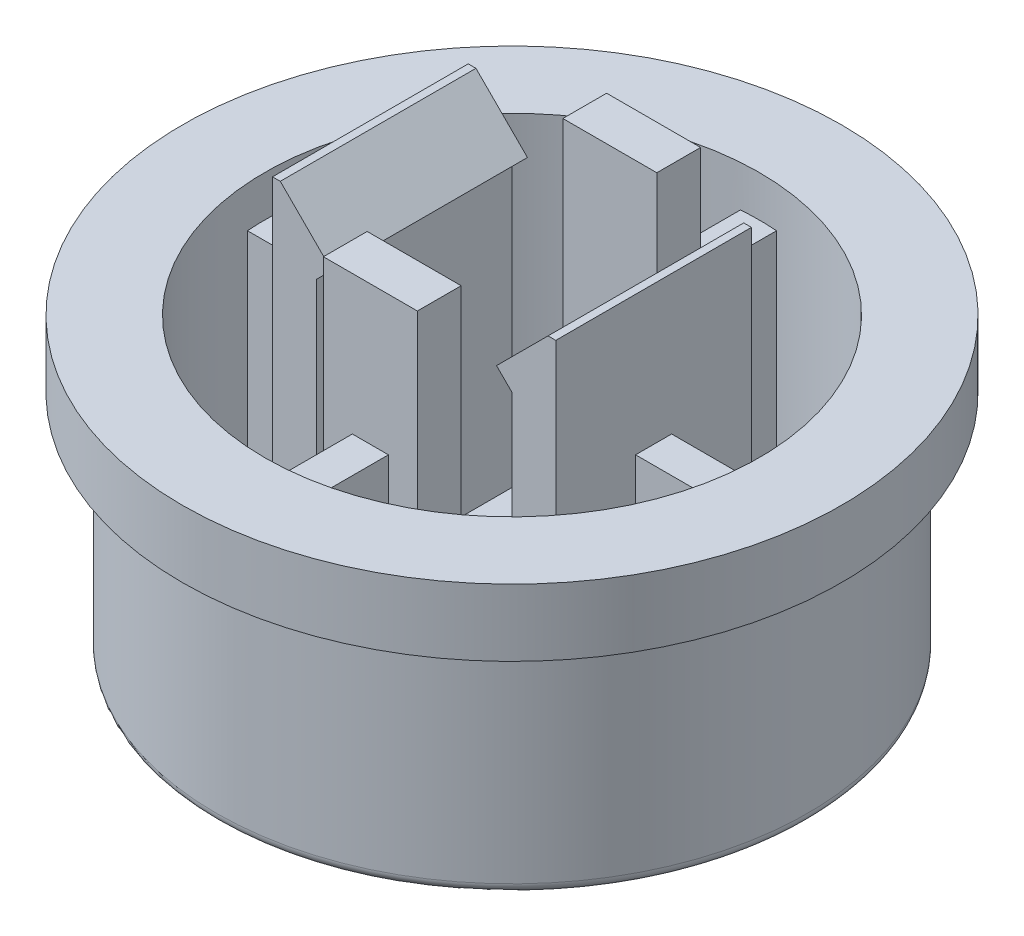
SolidWorks part; units mm, degrees
ref_plane "Front" through (0, 0, 0) normal (0, 0, 1) x (1, 0, 0)
ref_plane "Top" through (0, 0, 0) normal (0, 1, 0) x (1, 0, 0)
ref_plane "Right" through (0, 0, 0) normal (1, 0, 0) x (0, 0, -1)
sketch "Эскиз1" plane through (0, 0, 0) normal (0, 1, 0) x (1, 0, 0)
  circle A0 centre (0, 0) radius 5.75
extrude "Бобышка-Вытянуть1" add sketch "Эскиз1" along normal blind 0.9
sketch "Эскиз2" plane through (0, 0.9, 0) normal (0, 1, 0) x (1, 0, 0)
  circle A0 centre (0, 0) radius 5.75
  circle A1 centre (0, 0) radius 4.8
extrude "Бобышка-Вытянуть2" add sketch "Эскиз2" along normal blind 3.5
sketch "Эскиз3" plane through (0, 4.4, 0) normal (0, 1, 0) x (1, 0, 0)
  circle A0 centre (0, 0) radius 4.8
  circle A1 centre (0, 0) radius 6.4
extrude "Бобышка-Вытянуть3" add sketch "Эскиз3" along normal blind 1.3
sketch "Эскиз4" plane through (0, 0.9, 0) normal (0, 1, 0) x (1, 0, 0)
  line L2 (-2.75, -1.9) -> (-2.75, 1.9)
  line L4 (2.75, -1.9) -> (2.75, 1.9)
  line L8 (-1.9, -1.9) -> (-1.9, 1.9)
  line L10 (1.9, -1.9) -> (1.9, 1.9)
  line L11 (-0.9124, 1.9) -> (0.9124, 1.9)
  line L12 (-0.9124, 1.9) -> (-0.9124, 2.75)
  line L13 (-0.9124, 2.75) -> (0.9124, 2.75)
  line L14 (0.9124, 1.9) -> (0.9124, 2.75)
  line L15 (-0.9124, 1.9) -> (0.9124, 2.75) construction
  line L16 (-0.9124, 2.75) -> (0.9124, 1.9) construction
  line L17 (-1.9, 1.9) -> (-2.75, 1.9)
  line L18 (-0.9124, -2.75) -> (0.9124, -2.75)
  line L19 (-0.9124, -2.75) -> (-0.9124, -1.9)
  line L20 (-0.9124, -1.9) -> (0.9124, -1.9)
  line L21 (0.9124, -2.75) -> (0.9124, -1.9)
  line L22 (-0.9124, -2.75) -> (0.9124, -1.9) construction
  line L23 (-0.9124, -1.9) -> (0.9124, -2.75) construction
  line L24 (1.9, 1.9) -> (2.75, 1.9)
  line L25 (-1.9, -1.9) -> (-2.75, -1.9)
  line L26 (1.9, -1.9) -> (2.75, -1.9)
  point P0 (0, 0)
  point P6 (0, 0)
  point P15 (0, 2.325)
  point P22 (0, -2.325)
  dimension "D3" = 3.8
extrude "Бобышка-Вытянуть4" add sketch "Эскиз4" along normal blind 6.7
sketch "Эскиз5" plane through (0, 0, -1.9) normal (0, 0, -1) x (-1, 0, 0)
  line L9 (1.9, 7.6) -> (1.9, 0.9) construction
  line L10 (-1.9, 7.6) -> (-1.9, 0.9) construction
  line L11 (1.9, 6.3) -> (1.6, 6.6)
  line L12 (1.6, 6.6) -> (2.6, 7.6)
  line L13 (1.9, 7.6) -> (2.75, 7.6) construction
  line L14 (-1.9, 6.3) -> (-1.6, 6.6)
  line L15 (-1.6, 6.6) -> (-2.6, 7.6)
  line L16 (-2.75, 7.6) -> (-1.9, 7.6) construction
  line L17 (1.9, 6.3) -> (2.6, 7.6)
  line L18 (-1.9, 6.3) -> (-2.6, 7.6)
extrude "Бобышка-Вытянуть5" add sketch "Эскиз5" against normal blind 3.8
sketch "Эскиз6" plane through (0, 0, -1.9) normal (0, 0, -1) x (-1, 0, 0)
  line L0 (1.9, 6.9) -> (2.6, 7.6)
  line L1 (1.9, 7.6) -> (2.75, 7.6) construction
  line L2 (2.6, 7.6) -> (1.9, 7.6)
  line L3 (1.9, 7.6) -> (1.9, 6.9)
  line L4 (-1.9, 6.9) -> (-2.6, 7.6)
  line L5 (-2.75, 7.6) -> (-1.9, 7.6) construction
  line L6 (-2.6, 7.6) -> (-1.9, 7.6)
  line L7 (-1.9, 7.6) -> (-1.9, 6.9)
extrude "Вырез-Вытянуть1" cut sketch "Эскиз6" against normal up to next
sketch "Эскиз7" plane through (0, 0.9, 0) normal (0, 1, 0) x (1, 0, 0)
  line L0 (-0.35, -2.75) -> (0.35, -2.75)
  line L1 (4.7872, -0.35) -> (2.75, -0.35)
  line L2 (0.35, 2.75) -> (0.35, 4.7872)
  line L3 (4.7872, 0.35) -> (2.75, 0.35)
  line L4 (-0.35, 2.75) -> (-0.35, 4.7872)
  line L5 (-0.9124, -2.75) -> (0.9124, -2.75) construction
  line L6 (-0.9124, -2.75) -> (0.9124, -2.75) construction
  line L7 (-2.75, -0.35) -> (-4.7872, -0.35)
  line L8 (0.35, -4.7872) -> (0.35, -2.75)
  line L9 (-2.75, 0.35) -> (-4.7872, 0.35)
  line L10 (-0.35, -4.7872) -> (-0.35, -2.75)
  line L11 (-2.75, -0.35) -> (-2.75, 0.35)
  line L12 (-2.75, 1.9) -> (-2.75, -1.9) construction
  line L13 (-0.35, 2.75) -> (0.35, 2.75)
  line L14 (0.9124, 2.75) -> (-0.9124, 2.75) construction
  line L15 (2.75, -0.35) -> (2.75, 0.35)
  line L16 (2.75, -1.9) -> (2.75, 1.9) construction
  arc A0 (-0.35, -4.7872) -> (0.35, -4.7872) centre (0, 0) ccw
  arc A1 (-4.7872, 0.35) -> (-4.7872, -0.35) centre (0, 0) ccw
  arc A2 (0.35, 4.7872) -> (-0.35, 4.7872) centre (0, 0) ccw
  arc A3 (4.7872, -0.35) -> (4.7872, 0.35) centre (0, 0) ccw
extrude "Бобышка-Вытянуть6" add sketch "Эскиз7" along normal blind 4
fillet "Fillet1" radius 0.2 1 edges at (0, 0, 5.75)
